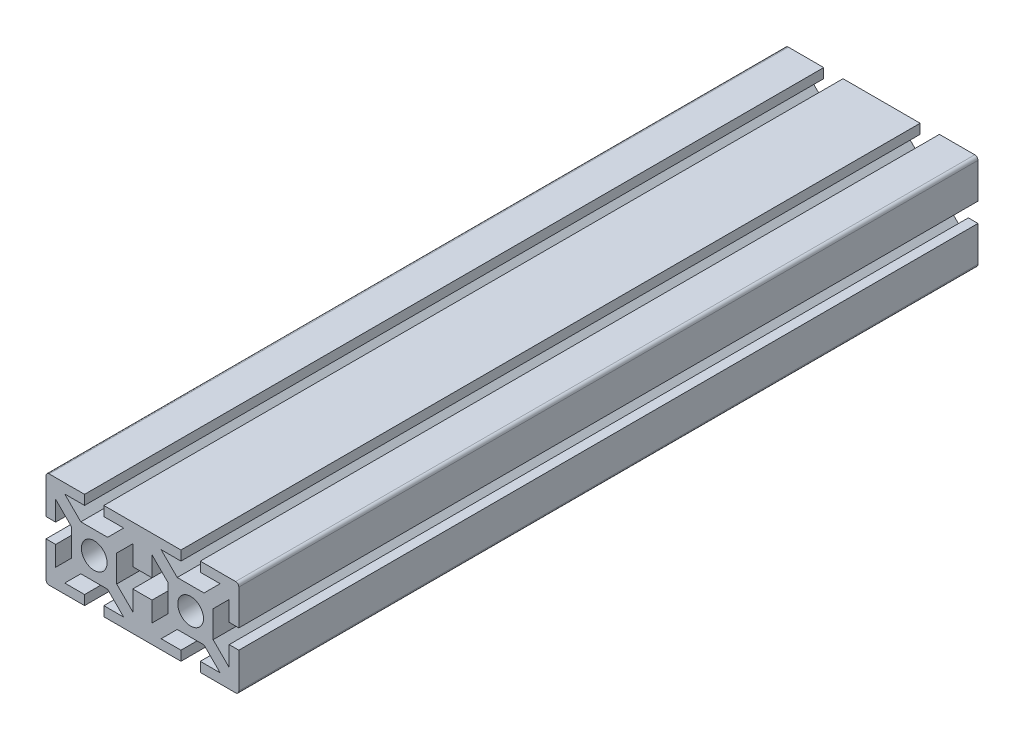
SolidWorks part; units mm, degrees
ref_plane "Alzado" through (0, 0, 0) normal (0, 0, 1) x (1, 0, 0)
ref_plane "Planta" through (0, 0, 0) normal (0, 1, 0) x (1, 0, 0)
ref_plane "Vista lateral" through (0, 0, 0) normal (1, 0, 0) x (0, 0, -1)
sketch "Croquis1" plane through (0, 0, 0) normal (0, 0, 1) x (1, 0, 0)
  line L0 (0, 0) -> (50000, 0) construction
  line L1 (-15, 15) -> (45, 15) construction
  line L2 (-15, 15) -> (-15, -15) construction
  line L3 (-15, -15) -> (15, -15) construction
  line L4 (15, 15) -> (15, -15) construction
  line L5 (-15, 15) -> (15, -15) construction
  line L6 (-15, -15) -> (15, 15) construction
  line L7 (0, 0) -> (0, -50000) construction
  line L9 (-4.1716, 7) -> (4.1716, 7)
  line L10 (4.1716, 7) -> (9.1716, 12)
  line L11 (9.1716, 12) -> (3, 12)
  line L12 (3, 12) -> (3, 15)
  line L13 (3, 15) -> (27, 15)
  line L22 (-3, 15) -> (-15, 15)
  line L23 (-3, 12) -> (-3, 15)
  line L24 (-9.1716, 12) -> (-3, 12)
  line L25 (-4.1716, 7) -> (-9.1716, 12)
  line L26 (7, 4.1716) -> (7, -4.1716)
  line L27 (7, -4.1716) -> (12, -9.1716)
  line L28 (12, -9.1716) -> (12, -3)
  line L29 (12, -3) -> (18, -3)
  line L34 (12, 3) -> (18, 3)
  line L35 (12, 9.1716) -> (12, 3)
  line L36 (7, 4.1716) -> (12, 9.1716)
  line L37 (15, 15) -> (15, -15) construction
  line L38 (4.1716, -7) -> (-4.1716, -7)
  line L39 (-4.1716, -7) -> (-9.1716, -12)
  line L40 (-9.1716, -12) -> (-3, -12)
  line L41 (-3, -12) -> (-3, -15)
  line L42 (-3, -15) -> (-15, -15)
  line L45 (3, -15) -> (27, -15)
  line L46 (3, -12) -> (3, -15)
  line L47 (9.1716, -12) -> (3, -12)
  line L48 (4.1716, -7) -> (9.1716, -12)
  line L49 (45, -15) -> (-15, -15) construction
  line L50 (-7, -4.1716) -> (-7, 4.1716)
  line L51 (-7, 4.1716) -> (-12, 9.1716)
  line L52 (-12, 9.1716) -> (-12, 3)
  line L53 (-12, 3) -> (-15, 3)
  line L54 (-15, 3) -> (-15, 15)
  line L57 (-15, -3) -> (-15, -15)
  line L58 (-12, -3) -> (-15, -3)
  line L59 (-12, -9.1716) -> (-12, -3)
  line L60 (-7, -4.1716) -> (-12, -9.1716)
  line L61 (-15, -15) -> (-15, 15) construction
  line L63 (45, -15) -> (45, 15) construction
  line L64 (45, -15) -> (15, 15) construction
  line L65 (45, 15) -> (15, -15) construction
  line L66 (45, -15) -> (15, -15) construction
  line L67 (45, 15) -> (45, -15) construction
  line L68 (37, -4.1716) -> (42, -9.1716)
  line L69 (42, -9.1716) -> (42, -3)
  line L70 (42, -3) -> (45, -3)
  line L71 (45, -3) -> (45, -15)
  line L72 (45, 3) -> (45, 15)
  line L73 (42, 3) -> (45, 3)
  line L74 (42, 9.1716) -> (42, 3)
  line L75 (37, 4.1716) -> (42, 9.1716)
  line L76 (37, -4.1716) -> (37, 4.1716)
  line L77 (25.8284, -7) -> (20.8284, -12)
  line L78 (20.8284, -12) -> (27, -12)
  line L79 (27, -12) -> (27, -15)
  line L80 (33, -15) -> (45, -15)
  line L81 (33, -12) -> (33, -15)
  line L82 (39.1716, -12) -> (33, -12)
  line L83 (34.1716, -7) -> (39.1716, -12)
  line L84 (25.8284, -7) -> (34.1716, -7)
  line L85 (23, 4.1716) -> (18, 9.1716)
  line L86 (18, 9.1716) -> (18, 3)
  line L87 (18, -9.1716) -> (18, -3)
  line L88 (23, -4.1716) -> (18, -9.1716)
  line L89 (23, 4.1716) -> (23, -4.1716)
  line L90 (34.1716, 7) -> (39.1716, 12)
  line L91 (39.1716, 12) -> (33, 12)
  line L92 (33, 12) -> (33, 15)
  line L93 (33, 15) -> (45, 15)
  line L94 (27, 12) -> (27, 15)
  line L95 (20.8284, 12) -> (27, 12)
  line L96 (25.8284, 7) -> (20.8284, 12)
  line L97 (34.1716, 7) -> (25.8284, 7)
  arc A0 (2.8284, 2.8284) -> (-2.8284, 2.8284) centre (0, 0) ccw
  arc A1 (2.8284, -2.8284) -> (2.8284, 2.8284) centre (0, 0) ccw
  arc A2 (-2.8284, -2.8284) -> (2.8284, -2.8284) centre (0, 0) ccw
  arc A3 (-2.8284, 2.8284) -> (-2.8284, -2.8284) centre (0, 0) ccw
  arc A4 (32.8284, 2.8284) -> (32.8284, -2.8284) centre (30, 0) cw
  arc A5 (32.8284, -2.8284) -> (27.1716, -2.8284) centre (30, 0) cw
  arc A6 (27.1716, -2.8284) -> (27.1716, 2.8284) centre (30, 0) cw
  arc A7 (27.1716, 2.8284) -> (32.8284, 2.8284) centre (30, 0) cw
  point P0 (0, 0)
  point P22 (0, 7)
  point P37 (7, 0)
  point P50 (0, -7)
  point P63 (-7, 0)
  point P64 (0, 0)
  point P93 (37, 0)
  point P94 (30, -7)
  point P95 (23, 0)
  point P96 (30, 7)
  dimension "D3" = 4
  dimension "D1" = 30
  dimension "D2" = 6
  dimension "D4" = 8
  dimension "D5" = 3
extrude "Saliente-Extruir1" add sketch "Croquis1" along normal mid plane 230
fillet "Redondeo1" radius 1 4 edges at (-15, -15, 0) (45, -15, 0) (45, 15, 0) (-15, 15, 0)
